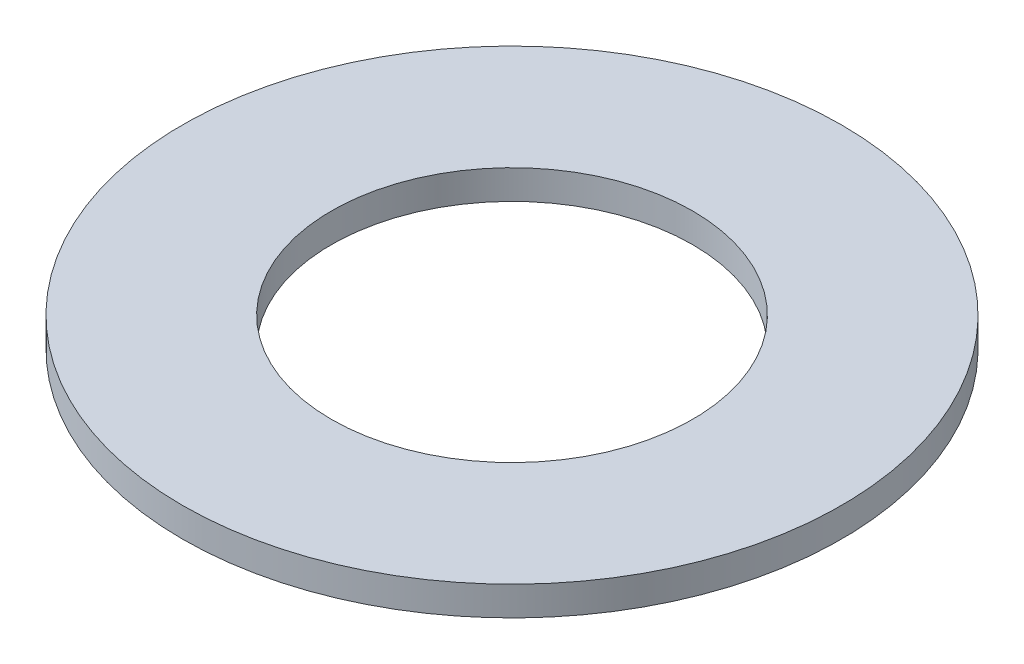
SolidWorks part; units mm, degrees
ref_plane "Front Plane" through (0, 0, 0) normal (0, 0, 1) x (1, 0, 0)
ref_plane "Top Plane" through (0, 0, 0) normal (0, 1, 0) x (1, 0, 0)
ref_plane "Right Plane" through (0, 0, 0) normal (1, 0, 0) x (0, 0, -1)
sketch "Sketch1" plane through (0, 0, 0) normal (0, 1, 0) x (1, 0, 0)
  circle A0 centre (0, 0) radius 20.8788
  circle A1 centre (0, 0) radius 38.1
  dimension "D1" = 41.7576
  dimension "D2" = 76.2
extrude "Boss-Extrude1" add sketch "Sketch1" along normal blind 3.3782
